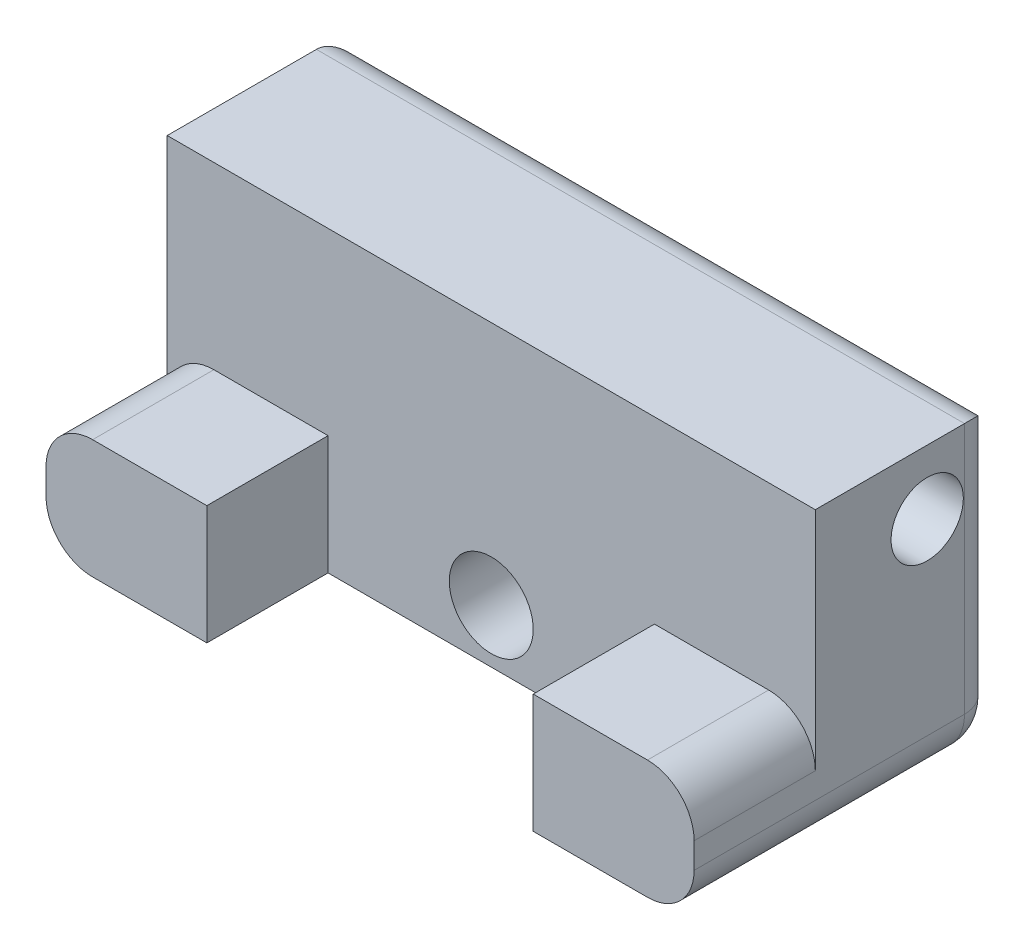
SolidWorks part; units mm, degrees
ref_plane "Front Plane" through (0, 0, 0) normal (0, 0, 1) x (1, 0, 0)
ref_plane "Top Plane" through (0, 0, 0) normal (0, 1, 0) x (1, 0, 0)
ref_plane "Right Plane" through (0, 0, 0) normal (1, 0, 0) x (0, 0, -1)
sketch "Sketch1" plane through (0, 0, 0) normal (1, 0, 0) x (0, 0, -1)
  line L0 (0, 0) -> (13, 0)
  line L1 (13, 0) -> (13, 13.5)
  line L2 (13, 13.5) -> (5.2, 13.5)
  line L3 (5.2, 13.5) -> (5.2, 5.8)
  line L4 (5.2, 5.8) -> (0, 5.8)
  line L5 (0, 5.8) -> (0, 0)
  circle A0 centre (10, 10.75) radius 1.55
  dimension "D5" = 3.1
  dimension "D1" = 7.8
  dimension "D2" = 13
  dimension "D3" = 5.8
  dimension "D4" = 13.5
  dimension "D6" = 3
  dimension "D7" = 2.75
extrude "Boss-Extrude1" add sketch "Sketch1" along normal blind 27.8
sketch "Sketch2" plane through (0, 5.8, 0) normal (0, 1, 0) x (1, 0, 0)
  line L0 (27.8, 5.2) -> (0, 5.2) construction
  line L1 (6.9, 5.2) -> (20.9, 5.2)
  line L2 (6.9, 5.2) -> (6.9, 0)
  line L3 (6.9, 0) -> (20.9, 0)
  line L4 (20.9, 5.2) -> (20.9, 0)
  line L5 (6.9, 5.2) -> (20.9, 0) construction
  line L6 (6.9, 0) -> (20.9, 5.2) construction
  line L7 (27.8, 0) -> (0, 0) construction
  line L10 (0, 0) -> (6.9, 0) construction
  line L11 (20.9, 0) -> (27.8, 0) construction
  point P4 (13.9, 2.6)
  dimension "D1" = 14
extrude "Cut-Extrude1" cut sketch "Sketch2" against normal through all
hole_wizard "CBORE for M3 Hex Socket Head Cap Screw1" positions "Sketch4" profile "Sketch5" counterbore size "M3" standard "DIN" end condition through all
sketch "Sketch4" plane through (0, 0, -13) normal (0, 0, -1) x (-1, 0, 0)
  line L0 (-27.8, 0) -> (-27.8, 13.5) construction
  line L1 (-27.8, 0) -> (0, 0) construction
  point P0 (-13.9, 3)
  dimension "D1" = 13.9
  dimension "D2" = 3
sketch "Sketch5" plane through (13.9, 3, -13) normal (1, 0, 0) x (0, 1, 0)
  line L0 (0, 0) -> (0, 13)
  line L1 (0, 13) -> (1.8, 13)
  line L3 (1.8, 13) -> (1.8, 3.4)
  line L4 (1.8, 3.4) -> (3.25, 3.4)
  line L5 (3.25, 3.4) -> (3.25, 0)
  line L7 (3.25, 0) -> (0, 0)
  line L11 (0, -6.35) -> (0, 107.95) construction
  dimension "Thru Hole Dia." = 3.6
  dimension "Thru Hole Depth" = 13
  dimension "C'Bore Dia." = 6.5
  dimension "C'Bore Depth" = 3.4
sketch "Sketch6" plane through (0, 0, 0) normal (0, -1, 0) x (1, 0, 0)
  line L1 (0, -13) -> (27.8, -13)
  line L2 (0, -13) -> (0, 0)
  line L3 (0, 0) -> (27.8, 0)
  line L4 (27.8, -13) -> (27.8, 0)
  line L5 (0, -13) -> (27.8, 0) construction
  line L6 (0, 0) -> (27.8, -13) construction
  point P4 (13.9, -6.5)
extrude "Cut-Extrude2" cut sketch "Sketch6" against normal blind 0.7
fillet "Fillet1" radius 2 4 edges at (27.8, 5.8, -2.6) (27.8, 0.7, -6.5) (0, 5.8, -2.6) (0, 0.7, -6.5)
fillet "Fillet2" radius 1.4 8 edges at (13.9, 13.5, -13) (0, 8.1, -13) (0.5858, 1.2858, -13) (6.8019, 0.7, -13) (13.9, 6.25, -13) (20.9981, 0.7, -13) (27.2142, 1.2858, -13) (27.8, 8.1, -13)
